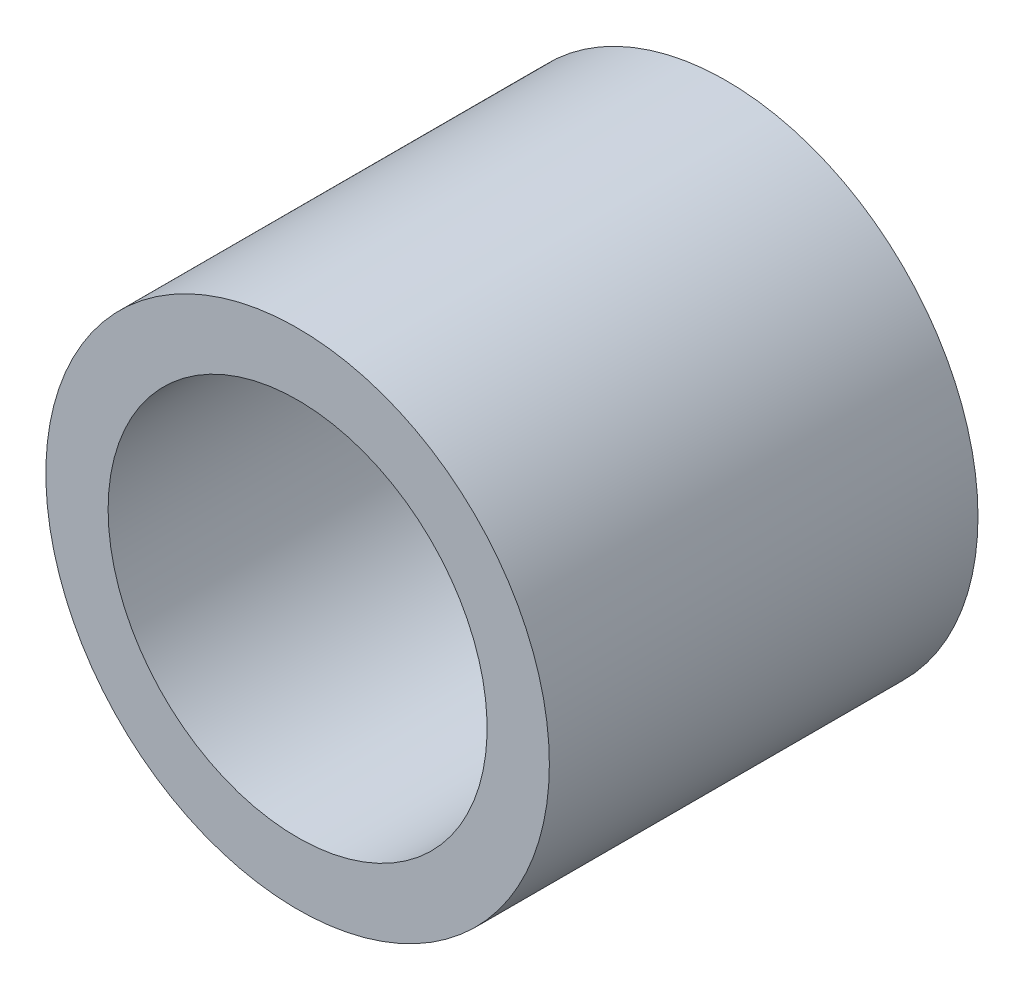
SolidWorks part; units mm, degrees
material "VITON"
ref_plane "Alzado" through (0, 0, 0) normal (0, 0, 1) x (1, 0, 0)
ref_plane "Planta" through (0, 0, 0) normal (0, 1, 0) x (1, 0, 0)
ref_plane "Vista lateral" through (0, 0, 0) normal (1, 0, 0) x (0, 0, -1)
sketch "Croquis2" plane through (0, 0, 0) normal (0, 0, 1) x (1, 0, 0)
  circle A0 centre (0, 0) radius 27.9
  dimension "D1" = 55.8
extrude "Saliente-Extruir1" add sketch "Croquis2" along normal blind 47.5
sketch "Croquis3" plane through (0, 0, 0) normal (0, 0, -1) x (-1, 0, 0)
  circle A0 centre (0, 0) radius 21
  dimension "D1" = 42
extrude "Cortar-Extruir1" cut sketch "Croquis3" against normal blind 47.5 contours A0
